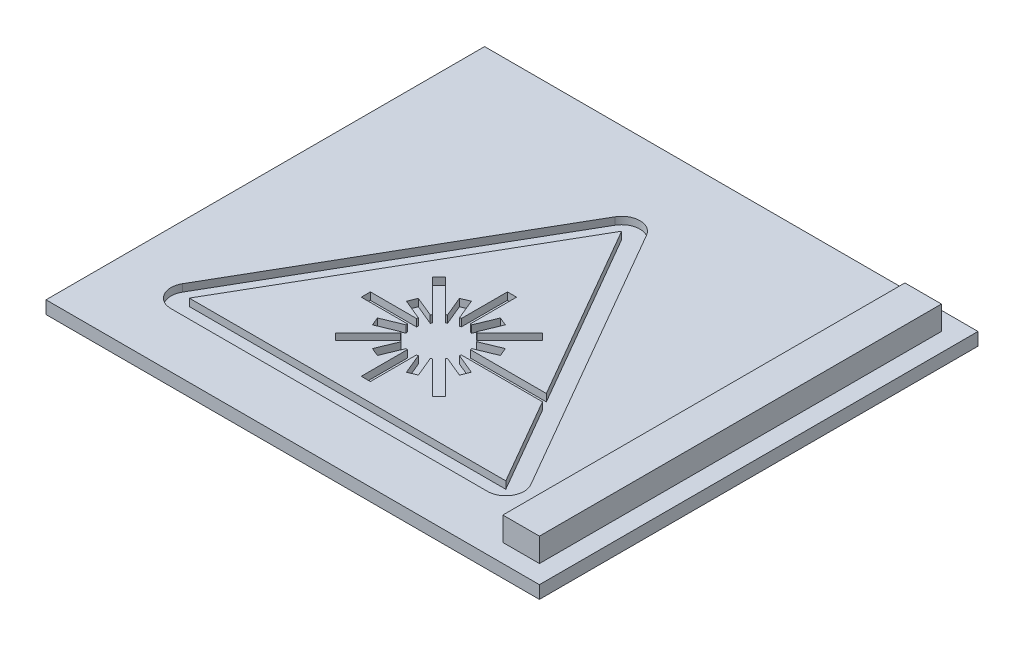
SolidWorks part; units mm, degrees
ref_plane "Front Plane" through (0, 0, 0) normal (0, 0, 1) x (1, 0, 0)
ref_plane "Top Plane" through (0, 0, 0) normal (0, 1, 0) x (1, 0, 0)
ref_plane "Right Plane" through (0, 0, 0) normal (1, 0, 0) x (0, 0, -1)
sketch "Sketch1" plane through (0, 0, 0) normal (0, 1, 0) x (1, 0, 0)
  line L0 (0, 0) -> (1, 0) construction
  line L5 (13, -12) -> (-13, -12)
  line L6 (13, -12) -> (13, 12)
  line L7 (13, 12) -> (-13, 12)
  line L8 (-13, -12) -> (-13, 12)
  line L9 (13, -12) -> (-13, 12) construction
  line L10 (13, 12) -> (-13, -12) construction
  line L12 (12, -11) -> (-10, -11) construction
  line L13 (12, -11) -> (12, 11) construction
  line L14 (12, 11) -> (-10, 11) construction
  line L15 (-10, -11) -> (-10, 11) construction
  line L16 (12, -11) -> (-10, 11) construction
  line L17 (12, 11) -> (-10, -11) construction
  point P0 (0, 0)
  dimension "D1" = 22
  dimension "D2" = 1
  dimension "D3" = 1
  dimension "D4" = 3
extrude "Boss-Extrude1" add sketch "Sketch1" along normal blind 0.7
sketch "Sketch2" plane through (0, 0.7, 0) normal (0, 1, 0) x (1, 0, 0)
  line L0 (0, 0) -> (11, 0) construction
  line L2 (12, -11) -> (10, -11)
  line L3 (12, -11) -> (12, 11)
  line L4 (12, 11) -> (10, 11)
  line L5 (10, -11) -> (10, 11)
  line L6 (12, -11) -> (10, 11) construction
  line L7 (12, 11) -> (10, -11) construction
  line L8 (13, 12) -> (-13, 12) construction
  line L9 (13, -12) -> (13, 12) construction
  dimension "D1" = 1
  dimension "D2" = 2
  dimension "D3" = 1
extrude "Boss-Extrude2" add sketch "Sketch2" along normal blind 1.3
sketch "Sketch3" plane through (0, 0.7, 0) normal (0, 1, 0) x (1, 0, 0)
  line L0 (-2.366, 7.5) -> (-11.0263, -7.5)
  line L1 (-10.1603, -9) -> (7.1603, -9)
  line L2 (8.0263, -7.5) -> (-0.634, 7.5)
  line L3 (-1.5, 9) -> (-1.5, 12) construction
  line L4 (13, 12) -> (-13, 12) construction
  line L5 (-1.5, -9) -> (-1.5, -12) construction
  line L6 (-13, -12) -> (13, -12) construction
  line L7 (-13, -9) -> (-11.8923, -9) construction
  line L9 (8.8923, -9) -> (10, -9) construction
  line L11 (7.1603, -8) -> (-1.5, 7)
  line L12 (-1.5, 7) -> (-10.1603, -8)
  line L13 (-10.1603, -8) -> (7.1603, -8)
  line L14 (-13, 12) -> (-13, -12) construction
  line L15 (10, 11) -> (10, -11) construction
  arc A0 (8.0263, -7.5) -> (7.1603, -9) centre (7.1603, -8) cw
  arc A1 (-10.1603, -9) -> (-11.0263, -7.5) centre (-10.1603, -8) cw
  arc A2 (-0.634, 7.5) -> (-2.366, 7.5) centre (-1.5, 7) ccw
  arc A3 (-1.5, 7) -> (-1.5, 7) centre (-1.5, 7) ccw
  arc A4 (-10.1603, -8) -> (-10.1603, -8) centre (-10.1603, -8) cw
  arc A5 (7.1603, -8) -> (7.1603, -8) centre (7.1603, -8) cw
  point P2 (0, 0.999)
  dimension "D1" = 1
  dimension "D3" = 3
  dimension "D2" = 1
extrude "Cut-Extrude2" cut sketch "Sketch3" against normal blind 0.4 contours A2 L0 A1 L1 A0 L2
sketch "Sketch5" plane through (0, 0.7, 0) normal (0, 1, 0) x (1, 0, 0)
  line L0 (7.1603, -8) -> (-0.201, -3.75) construction
  line L1 (-1.5, 7) -> (-10.1603, -8) construction
  line L2 (-1.5, 7) -> (-1.5, 1) construction
  line L3 (-10.1603, -8) -> (7.1603, -8) construction
  line L4 (-4.1517, -6.0052) -> (-2.369, -4.2226)
  line L7 (-1.25, 1) -> (-1.75, 1)
  line L8 (-1.75, -7) -> (-1.75, -4.479)
  line L9 (-1.5, -3) -> (-2.2942, -0.4292) construction
  line L11 (1.5052, -0.3483) -> (1.1517, 0.0052)
  line L12 (-4.5052, -5.6517) -> (-2.7226, -3.869)
  line L13 (-4.1517, -6.0052) -> (-4.5052, -5.6517)
  line L15 (2.5, -3.25) -> (2.5, -2.75)
  line L17 (-5.5, -3.25) -> (-5.5, -2.75)
  line L18 (-4.5052, -0.3483) -> (-2.7226, -2.131)
  line L19 (1.1517, -6.0052) -> (1.5052, -5.6517)
  line L20 (-4.1517, 0.0052) -> (-2.369, -1.7774)
  line L22 (-1.75, 1) -> (-1.75, -1.521)
  line L23 (-1.75, -7) -> (-1.25, -7)
  line L24 (-1.25, 1) -> (-1.25, -1.521)
  line L26 (1.1517, 0.0052) -> (-0.631, -1.7774)
  line L28 (1.5052, -0.3483) -> (-0.2774, -2.131)
  line L30 (2.5, -2.75) -> (-0.021, -2.75)
  line L32 (2.5, -3.25) -> (-0.021, -3.25)
  line L34 (1.5052, -5.6517) -> (-0.2774, -3.869)
  line L35 (-4.1517, 0.0052) -> (-4.5052, -0.3483)
  line L36 (1.1517, -6.0052) -> (-0.631, -4.2226)
  line L46 (-1.25, -4.479) -> (-1.25, -7)
  line L48 (-1.5, -7) -> (-1.5, -8) construction
  line L49 (-1.5, -3) -> (-2.7562, -0.6206) construction
  line L57 (-2.979, -3.25) -> (-5.5, -3.25)
  line L59 (-2.979, -2.75) -> (-5.5, -2.75)
  line L60 (-2.7562, -0.6206) -> (-2.2942, -0.4292)
  line L67 (-2.2942, -0.4292) -> (-1.75, -0.4292) construction
  line L68 (-2.7562, -0.6206) -> (-3.141, -1.0054) construction
  line L69 (-2.7562, -0.6206) -> (-2.297, -1.7292)
  line L79 (-2.2942, -0.4292) -> (-1.835, -1.5379)
  line L80 (-5.8301, -0.5) -> (7.1603, -8) construction
  line L82 (-1.5, -3) -> (-2.5252, -0.5249) construction
  line L83 (-1.5, -3) -> (-1.5, 1) construction
  line L84 (-0.7058, -0.4292) -> (-1.165, -1.5379)
  line L85 (-0.7058, -0.4292) -> (-0.2438, -0.6206)
  line L86 (-0.2438, -0.6206) -> (-0.703, -1.7292)
  line L87 (0.8794, -1.7438) -> (-0.2292, -2.203)
  line L88 (0.8794, -1.7438) -> (1.0708, -2.2058)
  line L89 (1.0708, -2.2058) -> (-0.0379, -2.665)
  line L90 (1.0708, -3.7942) -> (-0.0379, -3.335)
  line L91 (1.0708, -3.7942) -> (0.8794, -4.2562)
  line L92 (0.8794, -4.2562) -> (-0.2292, -3.797)
  line L93 (-0.2438, -5.3794) -> (-0.703, -4.2708)
  line L94 (-0.2438, -5.3794) -> (-0.7058, -5.5708)
  line L95 (-0.7058, -5.5708) -> (-1.165, -4.4621)
  line L96 (-2.2942, -5.5708) -> (-1.835, -4.4621)
  line L97 (-2.2942, -5.5708) -> (-2.7562, -5.3794)
  line L98 (-2.7562, -5.3794) -> (-2.297, -4.2708)
  line L99 (-3.8794, -4.2562) -> (-2.7708, -3.797)
  line L100 (-3.8794, -4.2562) -> (-4.0708, -3.7942)
  line L101 (-4.0708, -3.7942) -> (-2.9621, -3.335)
  line L102 (-4.0708, -2.2058) -> (-2.9621, -2.665)
  line L103 (-4.0708, -2.2058) -> (-3.8794, -1.7438)
  line L104 (-3.8794, -1.7438) -> (-2.7708, -2.203)
  arc A0 (-0.2774, -3.869) -> (-0.2292, -3.797) centre (-1.5, -3) ccw
  arc A1 (-1.25, -4.479) -> (-1.165, -4.4621) centre (-1.5, -3) ccw
  arc A2 (-2.369, -4.2226) -> (-2.297, -4.2708) centre (-1.5, -3) ccw
  arc A3 (-2.979, -3.25) -> (-2.9621, -3.335) centre (-1.5, -3) ccw
  arc A4 (-2.7226, -2.131) -> (-2.7708, -2.203) centre (-1.5, -3) ccw
  arc A5 (-0.021, -2.75) -> (-0.0379, -2.665) centre (-1.5, -3) ccw
  arc A6 (-0.631, -1.7774) -> (-0.703, -1.7292) centre (-1.5, -3) ccw
  arc A7 (-1.75, -1.521) -> (-1.835, -1.5379) centre (-1.5, -3) ccw
  arc A8 (-2.297, -1.7292) -> (-2.369, -1.7774) centre (-1.5, -3) ccw
  arc A9 (-1.165, -1.5379) -> (-1.25, -1.521) centre (-1.5, -3) ccw
  arc A10 (-0.2292, -2.203) -> (-0.2774, -2.131) centre (-1.5, -3) ccw
  arc A11 (-0.0379, -3.335) -> (-0.021, -3.25) centre (-1.5, -3) ccw
  arc A12 (-0.703, -4.2708) -> (-0.631, -4.2226) centre (-1.5, -3) ccw
  arc A13 (-1.835, -4.4621) -> (-1.75, -4.479) centre (-1.5, -3) ccw
  arc A14 (-2.7708, -3.797) -> (-2.7226, -3.869) centre (-1.5, -3) ccw
  arc A15 (-2.9621, -2.665) -> (-2.979, -2.75) centre (-1.5, -3) ccw
  point P10 (-1.5, -3)
  point P48 (-1.5, -3)
  point P103 (-1.5, -3)
  dimension "D1" = 3
  dimension "D5" = 1.2
  dimension "D6" = 22.5
  dimension "D4" = 8
  dimension "D7" = 8
extrude "Cut-Extrude3" cut sketch "Sketch5" against normal up to surface (0.4 mm away) up to face at (-1.5, 0.3, 3)
sketch "Sketch4" plane through (0, 0.7, 0) normal (0, 1, 0) x (1, 0, 0)
  line L0 (-13, -12) -> (13, -12) construction
  line L1 (-13, 12) -> (-14, 12)
  line L2 (-13, 12) -> (-13, -12)
  line L3 (-13, -12) -> (-14, -12)
  line L4 (-14, 12) -> (-14, -12)
  dimension "D1" = 1
extrude "Boss-Extrude3" add sketch "Sketch4" against normal up to surface (0.7 mm away) up to face at (0, 0, 0)
sketch "Sketch6" plane through (0, 0.7, 0) normal (0, 1, 0) x (1, 0, 0)
  line L0 (2.5, -2.75) -> (4.1292, -2.75)
  line L1 (7.1603, -8) -> (-1.5, 7) construction
  line L2 (2.5, -3.25) -> (4.4178, -3.25)
  line L3 (7.1603, -8) -> (-1.5, 7) construction
  line L4 (-0.021, -3.25) -> (2.5, -3.25) construction
  line L5 (2.5, -2.75) -> (-0.021, -2.75) construction
  line L6 (4.4178, -3.25) -> (4.1292, -2.75)
  line L7 (2.5, -3.25) -> (2.5, -2.75) construction
  line L8 (2.5, -3.25) -> (2.5, -2.75)
extrude "Cut-Extrude4" cut sketch "Sketch6" against normal up to surface (0.4 mm away) up to face at (-1.5, 0.3, 3)
